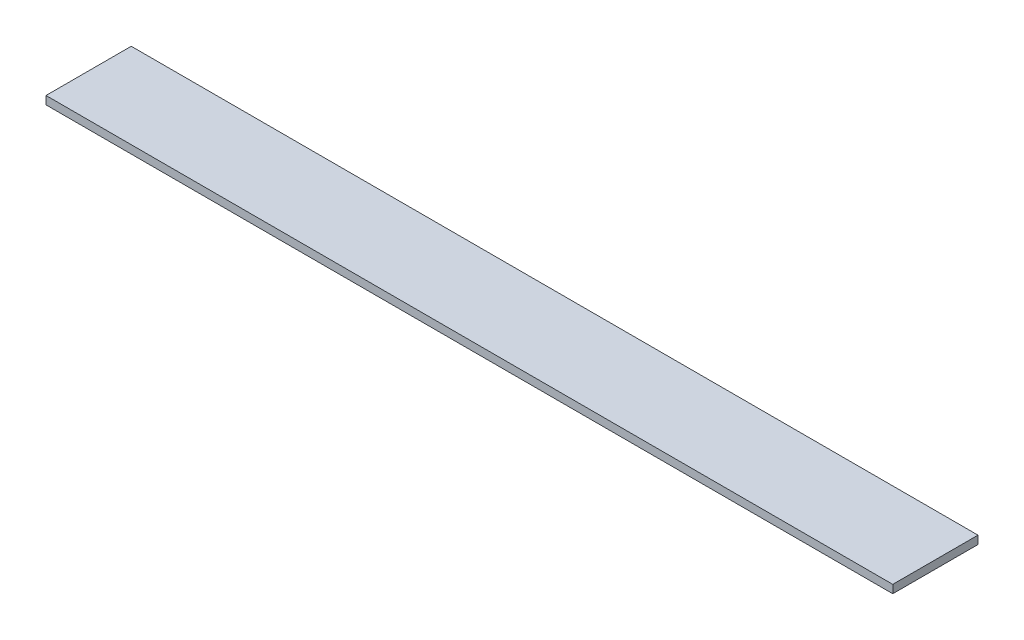
SolidWorks part; units mm, degrees
ref_plane "Front Plane" through (0, 0, 0) normal (0, 0, 1) x (1, 0, 0)
ref_plane "Top Plane" through (0, 0, 0) normal (0, 1, 0) x (1, 0, 0)
ref_plane "Right Plane" through (0, 0, 0) normal (1, 0, 0) x (0, 0, -1)
sketch "Sketch1" plane through (0, 0, 0) normal (0, 1, 0) x (1, 0, 0)
  line L1 (-63.0796, -6.35) -> (63.0796, -6.35)
  line L2 (-63.0796, -6.35) -> (-63.0796, 6.35)
  line L3 (-63.0796, 6.35) -> (63.0796, 6.35)
  line L4 (63.0796, -6.35) -> (63.0796, 6.35)
  line L5 (-63.0796, -6.35) -> (63.0796, 6.35) construction
  line L6 (-63.0796, 6.35) -> (63.0796, -6.35) construction
  point P0 (0, 0)
  dimension "D1" = 126.1593
  dimension "D2" = 12.7
extrude "Boss-Extrude1" add sketch "Sketch1" along normal blind 1.2141
